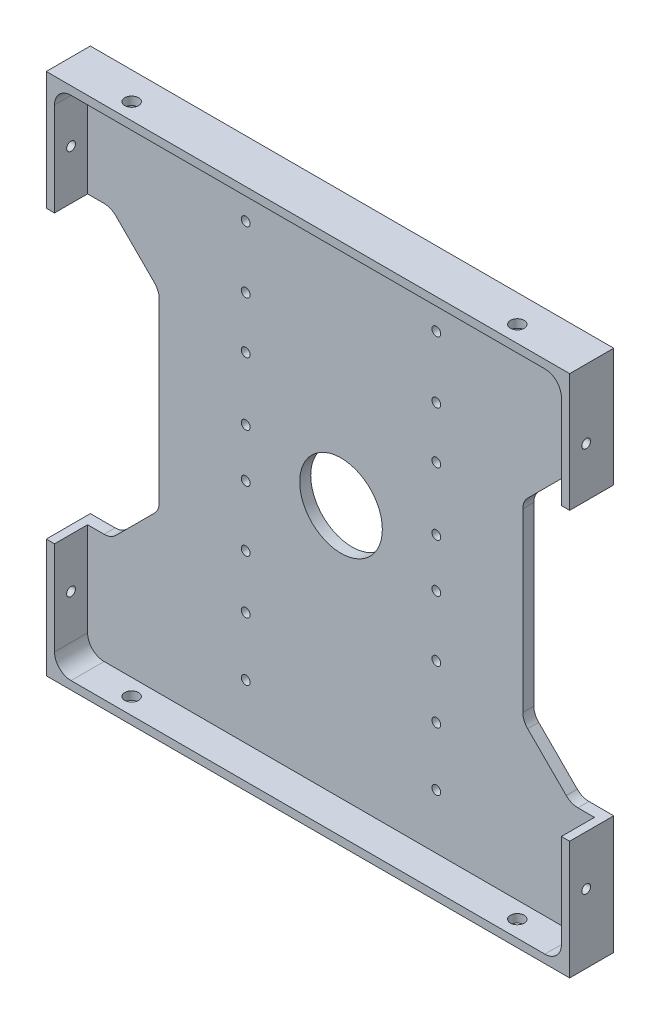
SolidWorks part; units mm, degrees
material "6061-T6 (SS)"
ref_plane "Front" through (0, 0, 0) normal (0, 0, 1) x (1, 0, 0)
ref_plane "Top" through (0, 0, 0) normal (0, 1, 0) x (1, 0, 0)
ref_plane "Right" through (0, 0, 0) normal (1, 0, 0) x (0, 0, -1)
sketch "Sketch1" plane through (0, 0, 0) normal (0, 0, 1) x (1, 0, 0)
  line L1 (-48, -48) -> (48, -48)
  line L2 (-48, -48) -> (-48, 48)
  line L3 (-48, 48) -> (48, 48)
  line L4 (48, -48) -> (48, 48)
  line L5 (-48, -48) -> (48, 48) construction
  line L6 (-48, 48) -> (48, -48) construction
  point P0 (0, 0)
  dimension "D1" = 96
  dimension "D2" = 96
extrude "Boss-Extrude1" add sketch "Sketch1" along normal blind 8
sketch "Sketch2" plane through (0, 0, 8) normal (0, 0, 1) x (1, 0, 0)
  line L1 (46, -46) -> (-46, -46)
  line L2 (46, -46) -> (46, 46)
  line L3 (46, 46) -> (-46, 46)
  line L4 (-46, -46) -> (-46, 46)
  line L5 (46, -46) -> (-46, 46) construction
  line L6 (46, 46) -> (-46, -46) construction
  point P0 (0, 0)
  dimension "D1" = 92
  dimension "D2" = 92
extrude "Component Platform" cut sketch "Sketch2" against normal blind 6
sketch "Sketch3" plane through (0, 0, 2) normal (0, 0, 1) x (1, 0, 0)
  line L1 (-40.8787, -25.1213) -> (-33.8787, -18.1213)
  line L2 (-40.8787, 25.1213) -> (-33.8787, 18.1213)
  line L3 (-33, -16) -> (-33, 16)
  line L4 (-48, -26) -> (-43, -26)
  line L7 (-48, 48) -> (-48, -48) construction
  line L8 (0, -56.7987) -> (0, 73.4321) construction
  line L9 (46, -46) -> (-57.8147, 57.8147) construction
  line L18 (46, 46) -> (-68.5705, -68.5705) construction
  line L23 (-48, 26) -> (-43, 26)
  line L26 (-48, -26) -> (-48, 26)
  line L28 (-48, -48) -> (48, -48) construction
  line L29 (48, -26) -> (48, 26)
  line L30 (48, 26) -> (43, 26)
  line L31 (40.8787, 25.1213) -> (33.8787, 18.1213)
  line L32 (33, -16) -> (33, 16)
  line L33 (40.8787, -25.1213) -> (33.8787, -18.1213)
  line L34 (48, -26) -> (43, -26)
  arc A3 (-33.8787, -18.1213) -> (-33, -16) centre (-36, -16) ccw
  arc A4 (-33.8787, 18.1213) -> (-33, 16) centre (-36, 16) cw
  arc A13 (-40.8787, -25.1213) -> (-43, -26) centre (-43, -23) cw
  arc A15 (-40.8787, 25.1213) -> (-43, 26) centre (-43, 23) ccw
  arc A17 (40.8787, 25.1213) -> (43, 26) centre (43, 23) cw
  arc A18 (33.8787, 18.1213) -> (33, 16) centre (36, 16) ccw
  arc A19 (33.8787, -18.1213) -> (33, -16) centre (36, -16) cw
  arc A20 (40.8787, -25.1213) -> (43, -26) centre (43, -23) ccw
  point P0 (-48, 0)
  point P37 (-48, 0)
  dimension "D2" = 3
  dimension "D3" = 3
  dimension "D4" = 15
  dimension "D6" = 3
  dimension "D7" = 3
  dimension "D8" = 135
  dimension "D5" = 52
  dimension "D9" = 135
  dimension "D10" = 5
  dimension "D11" = 5
  dimension "D12" = 48
extrude "Cable Slots" cut sketch "Sketch3" against normal mid plane 12
sketch "Sketch4" plane through (0, 0, 2) normal (0, 0, 1) x (1, 0, 0)
  circle A0 centre (0, 0) radius 7.5
  dimension "D1" = 15
extrude "Center Mass Cut" cut sketch "Sketch4" against normal blind 6
ref_plane "Center Y-Plane" through (0, 0, 0) normal (1, 0, 0) x (0, 0, -1)
ref_plane "Center X-Plane" through (0, 0, 0) normal (0, -1, 0) x (-1, 0, 0)
fillet "Inner Corner Fillets" radius 3 4 edges at (46, -46, 5) (-46, -46, 5) (46, 46, 5) (-46, 46, 5)
sketch "Sketch8" plane through (48, 0, 0) normal (1, 0, 0) x (0, 0, -1)
  line L0 (-5, -48) -> (-5, 48) construction
  line L1 (-8, -48) -> (0, -48) construction
  line L2 (-8, 48) -> (0, 48) construction
  line L3 (-8, -48) -> (-8, -26) construction
  point P12 (-5, 35)
  point P13 (-5, -35)
  dimension "D1" = 3
  dimension "D2" = 13
  dimension "D3" = 83
sketch "Sketch11" plane through (0, -48, 0) normal (0, -1, 0) x (-1, 0, 0)
  line L0 (48, -5) -> (-48.0639, -5) construction
  line L1 (48, -8) -> (48, 0) construction
  line L2 (48, -8) -> (-48, -8) construction
  dimension "D1" = 3
hole_wizard "Tap Drill for M3x0.5 Tap4" positions "Sketch12" profile "Sketch13" hole size "M3x0.5" standard "ANSI Metric" end condition up to next
sketch "Sketch12" plane through (0, -48, 0) normal (0, -1, 0) x (-1, 0, 0)
  line L0 (48, -5) -> (-48.0639, -5) construction
  point P0 (35, -5)
  point P4 (-35, -5)
  dimension "D1" = 70
  dimension "D2" = 35
sketch "Sketch13" plane through (-35, -48, 5) normal (1, 0, 0) x (0, 0, -1)
  line L0 (0, 0) -> (0, 2)
  line L1 (0, 2) -> (1.25, 2)
  line L2 (1.25, 2) -> (1.25, 0)
  line L5 (1.25, 0) -> (0, 0)
  line L11 (0, -6.35) -> (0, 107.95) construction
  dimension "Thru Hole Dia." = 2.5
  dimension "Thru Hole Depth" = 2
mirror "Mirror2" about plane through (0, 0, 0) normal (0, -1, 0) of "Tap Drill for M3x0.5 Tap4"
sketch "Sketch14" plane through (0, 0, 2) normal (0, 0, 1) x (1, 0, 0)
  line L2 (-34.5286, 36.05) -> (20.3487, 36.05) construction
  line L4 (-17.3, 36.05) -> (-17.3, -36.05) construction
  line L5 (0, 0) -> (0, 36.05) construction
  point P2 (-17.3, -15.75)
  point P5 (-17.3, -4.75)
  point P7 (-17.3, 36.05)
  point P8 (-17.3, 15.45)
  point P9 (-17.3, 24.85)
  point P11 (-17.3, 4.05)
  point P13 (17.3, 4.05)
  point P14 (17.3, 15.45)
  point P15 (17.3, 24.85)
  point P16 (17.3, 36.05)
  point P17 (-17.3, -25.45)
  point P18 (-17.3, -36.05)
  point P30 (17.3, -36.05)
  point P31 (17.3, -25.45)
  point P32 (17.3, -15.75)
  point P33 (17.3, -4.75)
  point P35 (-17.3, 0)
  dimension "D1" = 17.3
  dimension "D2" = 72.1
  dimension "D3" = 10.6
  dimension "D4" = 20.3
  dimension "D5" = 31.3
  dimension "D6" = 40.1
  dimension "D7" = 51.5
  dimension "D8" = 60.9
hole_wizard "Tap Drill for M2x0.4 Tap2" positions "Sketch15" profile "Sketch17" hole size "M2x0.4" standard "ANSI Metric" end condition through all
sketch "Sketch15" plane through (0, 0, 2) normal (0, 0, 1) x (1, 0, 0)
  point P0 (-17.3, 36.05)
  point P3 (-17.3, 24.85)
  point P6 (-17.3, 15.45)
  point P9 (-17.3, 4.05)
  point P12 (17.3, 4.05)
  point P15 (17.3, 15.45)
  point P18 (17.3, 24.85)
  point P21 (17.3, 36.05)
  point P46 (17.3, -4.75)
  point P49 (17.3, -15.75)
  point P52 (17.3, -25.45)
  point P55 (17.3, -36.05)
  point P58 (-17.3, -4.75)
  point P61 (-17.3, -15.75)
  point P64 (-17.3, -25.45)
  point P67 (-17.3, -36.05)
sketch "Sketch17" plane through (-17.3, 36.05, 2) normal (1, 0, 0) x (0, -1, 0)
  line L0 (0, 0) -> (0, 2)
  line L1 (0, 2) -> (0.8, 2)
  line L2 (0.8, 2) -> (0.8, 0)
  line L5 (0.8, 0) -> (0, 0)
  line L11 (0, -6.35) -> (0, 107.95) construction
  dimension "Thru Hole Dia." = 1.6
  dimension "Thru Hole Depth" = 2
hole_wizard "Tap Drill for M2x0.4 Tap1" positions "Sketch26" profile "Sketch27" hole size "M2x0.4" standard "ANSI Metric" end condition up to next
sketch "Sketch26" plane through (48, 0, 0) normal (1, 0, 0) x (0, 0, -1)
  point P0 (-5, -35)
  point P3 (-5, 35)
sketch "Sketch27" plane through (48, -35, 5) normal (0, 1, 0) x (0, 0, -1)
  line L0 (0, 0) -> (0, 2)
  line L1 (0, 2) -> (0.8, 2)
  line L2 (0.8, 2) -> (0.8, 0)
  line L5 (0.8, 0) -> (0, 0)
  line L11 (0, -6.35) -> (0, 107.95) construction
  dimension "Thru Hole Dia." = 1.6
  dimension "Thru Hole Depth" = 2
mirror "Mirror3" about plane through (0, 0, 0) normal (1, 0, 0) of "Tap Drill for M2x0.4 Tap1"
sketch "Sketch28" plane through (0, 0, 0) normal (0, 0, -1) x (-1, 0, 0)
  line L1 (47.5, -47.5) -> (-47.5, -47.5)
  line L2 (47.5, -47.5) -> (47.5, 47.5)
  line L3 (47.5, 47.5) -> (-47.5, 47.5)
  line L4 (-47.5, -47.5) -> (-47.5, 47.5)
  line L5 (47.5, -47.5) -> (-47.5, 47.5) construction
  line L6 (47.5, 47.5) -> (-47.5, -47.5) construction
  point P0 (0, 0)
  dimension "D1" = 95
  dimension "D2" = 95
extrude "Cut-Extrude1" cut sketch "Sketch28" against normal up to next flip side to cut
equation "\"MountingBracketXYSideTolerance\"= - 0.5"
equation "\"D2@Sketch28\"=96mm + \"MountingBracketXYSideTolerance\"*2"
equation "\"D1@Sketch28\"=96.00mm+\"MountingBracketXYSideTolerance\"*2"
